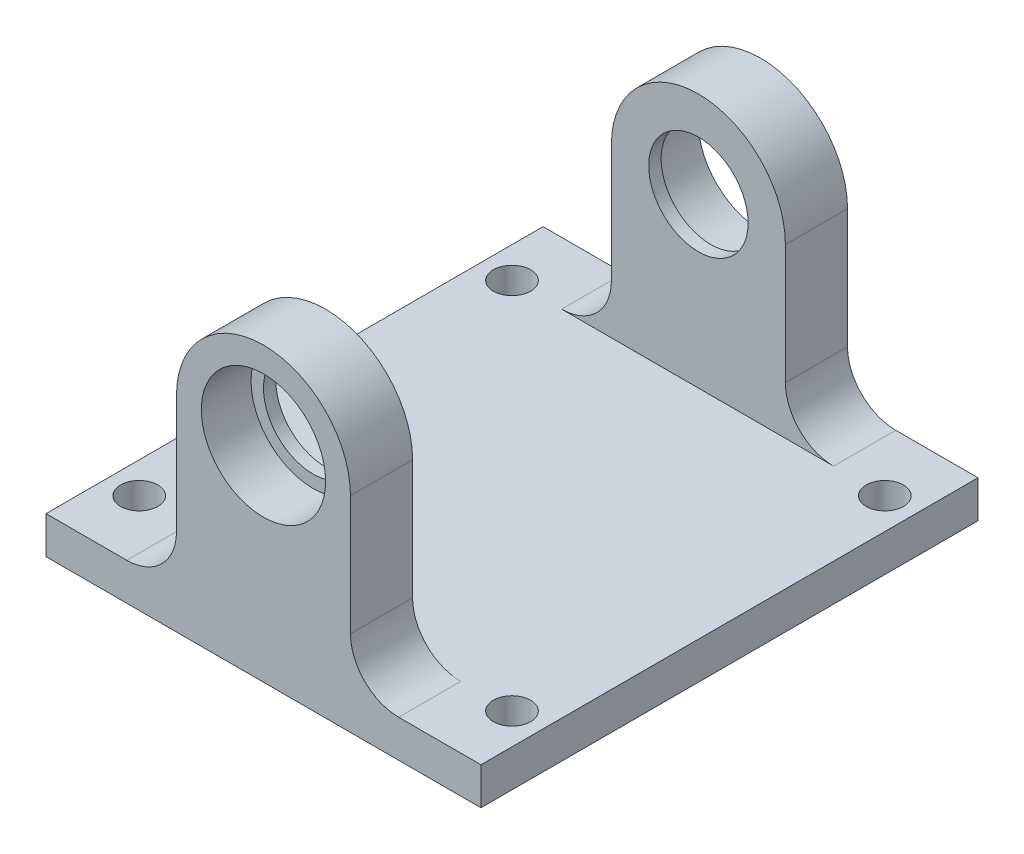
SolidWorks part; units mm, degrees
ref_plane "Alzado" through (0, 0, 0) normal (0, 0, 1) x (1, 0, 0)
ref_plane "Planta" through (0, 0, 0) normal (0, 1, 0) x (1, 0, 0)
ref_plane "Vista lateral" through (0, 0, 0) normal (1, 0, 0) x (0, 0, -1)
sketch "Croquis1" plane through (0, 0, 0) normal (0, 1, 0) x (1, 0, 0)
  line L0 (0, 0) -> (35, 0)
  line L1 (35, 0) -> (35, 40)
  line L2 (0, 0) -> (0, 40)
  line L3 (0, 40) -> (35, 40)
  circle A0 centre (2.5, 35) radius 1.5
  circle A1 centre (32.5, 35) radius 1.5
  circle A2 centre (32.5, 5) radius 1.5
  circle A3 centre (2.5, 5) radius 1.5
  dimension "D3" = 3
  dimension "D7" = 5
  dimension "D1" = 35
  dimension "D2" = 40
  dimension "D4" = 2.5
  dimension "D5" = 2
  dimension "D6" = 2
extrude "Saliente-Extruir1" add sketch "Croquis1" along normal blind 3
sketch "Croquis2" plane through (0, 0, 0) normal (0, 0, 1) x (1, 0, 0)
  line L2 (24.5, 16.5) -> (24.5, 6.8809)
  line L3 (10.5, 16.5) -> (10.5, 7)
  line L7 (6.5, 3) -> (28.3809, 3)
  circle A0 centre (17.5, 16.5) radius 5
  arc A1 (24.5, 16.5) -> (10.5, 16.5) centre (17.5, 16.5) ccw
  arc A2 (10.5, 7) -> (6.5, 3) centre (6.5, 7) cw
  arc A3 (24.5, 6.8809) -> (28.3809, 3) centre (28.3809, 6.8809) ccw
  circle A4 centre (17.5, 16.5) radius 7 construction
  dimension "D2" = 10
  dimension "D4" = 4
  dimension "D5" = 3.8809
  dimension "D3" = 2
extrude "Saliente-Extruir2" add sketch "Croquis2" against normal up to surface (40 mm away) up to face at (17.5, 1.5, -40)
sketch "Croquis3" plane through (0, 3, 0) normal (0, 1, 0) x (1, 0, 0)
  line L0 (4, 5) -> (31, 5)
  line L1 (31, 5) -> (31, 35)
  line L2 (31, 35) -> (4, 35)
  line L3 (4, 35) -> (4, 5)
  line L5 (35, 40) -> (28.3809, 40) construction
  line L6 (28.3809, 0) -> (35, 0) construction
  line L7 (35, 0) -> (35, 40) construction
  line L8 (0, 40) -> (0, 0) construction
  dimension "D1" = 5
  dimension "D2" = 5
  dimension "D3" = 4
  dimension "D4" = 4
extrude "Cortar-Extruir1" cut sketch "Croquis3" along normal through all
sketch "Croquis4" plane through (0, 0, -35) normal (0, 0, 1) x (1, 0, 0)
  circle A0 centre (17.5, 16.5) radius 5
  circle A1 centre (17.5, 16.5) radius 4
  dimension "D1" = 1
extrude "Saliente-Extruir3" add sketch "Croquis4" against normal blind 1
sketch "Croquis5" plane through (0, 0, -5) normal (0, 0, -1) x (-1, 0, 0)
  circle A0 centre (-17.5, 16.5) radius 5
  circle A1 centre (-17.5, 16.5) radius 4
  dimension "D1" = 1
extrude "Saliente-Extruir4" add sketch "Croquis5" against normal blind 1
